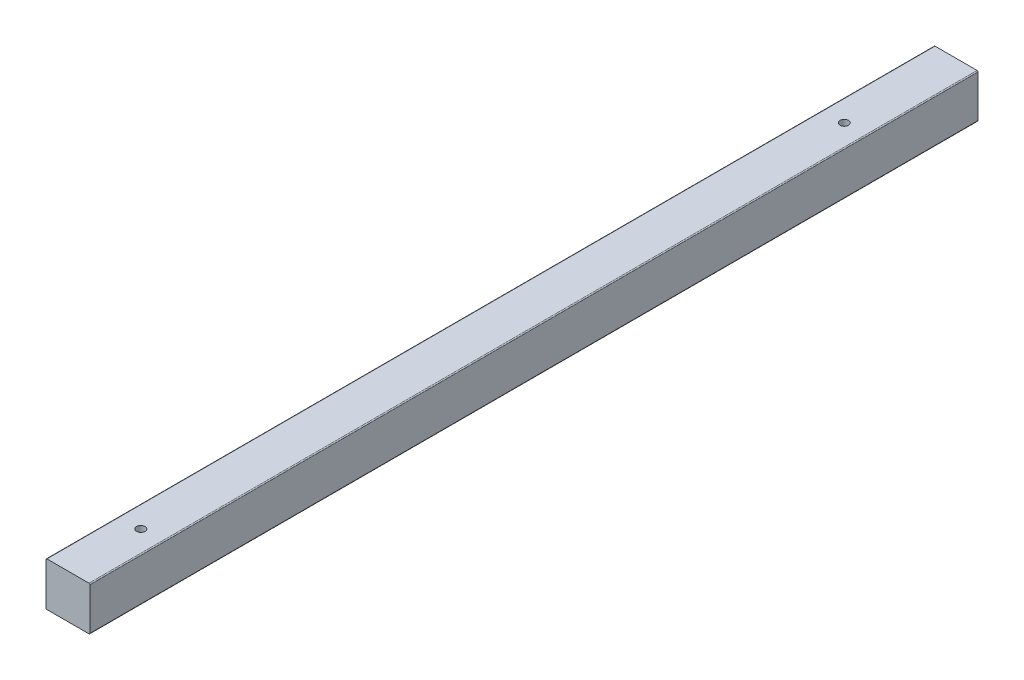
SolidWorks part; units mm, degrees
ref_plane "Front Plane" through (0, 0, 0) normal (0, 0, 1) x (1, 0, 0)
ref_plane "Top Plane" through (0, 0, 0) normal (0, 1, 0) x (1, 0, 0)
ref_plane "Right Plane" through (0, 0, 0) normal (1, 0, 0) x (0, 0, -1)
sketch "Sketch1" plane through (0, 0, 0) normal (0, 0, 1) x (1, 0, 0)
  line L1 (0, 0) -> (-44, 0)
  line L2 (0, 0) -> (0, 44)
  line L3 (0, 44) -> (-44, 44)
  line L4 (-44, 0) -> (-44, 44)
  dimension "D1" = 44
extrude "Boss-Extrude1" add sketch "Sketch1" along normal blind 890
fillet "Fillet1" radius 1 4 edges at (-44, 44, 445) (0, 44, 445) (-44, 0, 445) (0, 0, 445)
sketch "Sketch2" plane through (0, 0, 0) normal (0, -1, 0) x (1, 0, 0)
  line L0 (-43, 890) -> (-1, 890) construction
  circle A0 centre (-22, 817) radius 14
  circle A1 centre (-22, 112) radius 14
  point P6 (-22, 890)
  dimension "D3" = 28
  dimension "D1" = 705
  dimension "D2" = 73
extrude "Cut-Extrude1" cut sketch "Sketch2" against normal blind 8
sketch "Sketch3" plane through (0, 8, 0) normal (0, -1, 0) x (1, 0, 0)
  circle A0 centre (-22, 817) radius 4.25
  circle A1 centre (-22, 112) radius 4.25
  circle A2 centre (-22, 817) radius 14 construction
  dimension "D1" = 8.5
extrude "Cut-Extrude2" cut sketch "Sketch3" against normal through all
